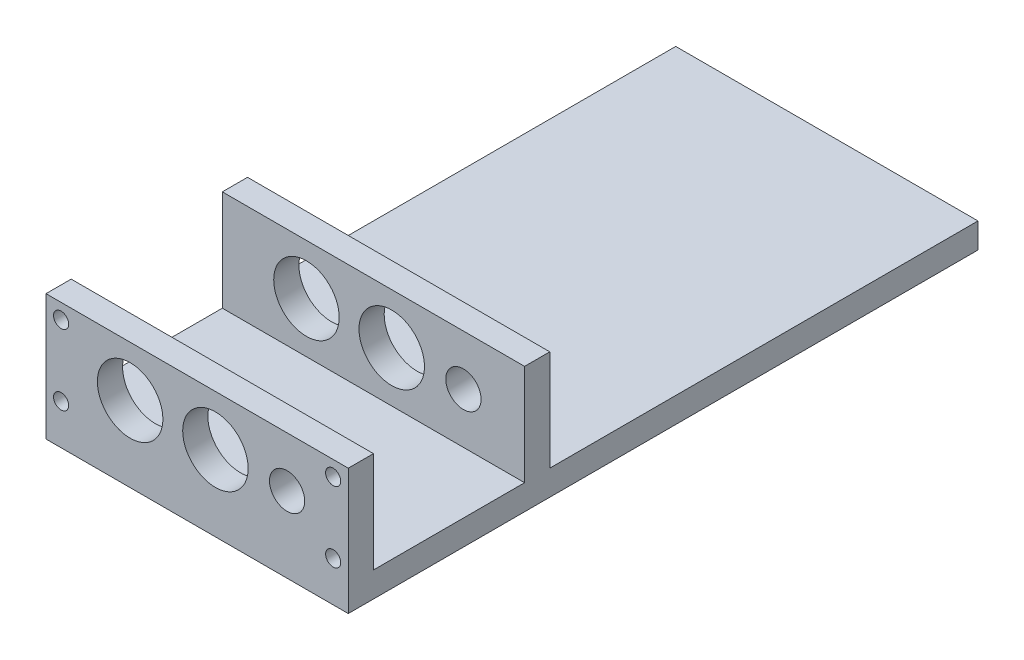
SolidWorks part; units mm, degrees
ref_plane "정면" through (0, 0, 0) normal (0, 0, 1) x (1, 0, 0)
ref_plane "윗면" through (0, 0, 0) normal (0, 1, 0) x (1, 0, 0)
ref_plane "우측면" through (0, 0, 0) normal (1, 0, 0) x (0, 0, -1)
sketch "스케치1" plane through (0, 0, 0) normal (0, 0, 1) x (1, 0, 0)
  line L0 (0, 0) -> (60, 0)
  line L3 (0, 0) -> (0, 25)
  line L4 (0, 25) -> (60, 25)
  line L5 (60, 0) -> (60, 25)
  dimension "D1" = 60
  dimension "D2" = 25
extrude "보스-돌출1" add sketch "스케치1" along normal blind 5
sketch "스케치2" plane through (0, 0, 0) normal (0, 0, -1) x (-1, 0, 0)
  line L0 (-60, 0) -> (-60, 25) construction
  line L1 (-60, 5) -> (0, 5)
  line L2 (-60, 5) -> (-60, 0)
  line L3 (-60, 0) -> (0, 0)
  line L4 (0, 5) -> (0, 0)
  dimension "D1" = 5
extrude "보스-돌출2" add sketch "스케치2" along normal blind 120
sketch "스케치3" plane through (0, 5, 0) normal (0, 1, 0) x (1, 0, 0)
  line L0 (60, 35) -> (0, 35)
  line L1 (60, 120) -> (60, 0) construction
  line L2 (0, 120) -> (0, 0) construction
  line L3 (0, 35) -> (0, 30)
  line L4 (0, 30) -> (60, 30)
  line L5 (60, 30) -> (60, 35)
  line L6 (60, -5) -> (0, -5) construction
  dimension "D1" = 40
  dimension "D2" = 5
extrude "보스-돌출3" add sketch "스케치3" along normal blind 20
sketch "스케치4" plane through (0, 0, 0) normal (0, 0, -1) x (-1, 0, 0)
  line L0 (-60, 5) -> (-60, 25) construction
  line L2 (-60, 15) -> (0, 15) construction
  line L3 (0, 25) -> (0, 5) construction
  line L4 (-30, 5) -> (-30, 25) construction
  line L5 (0, 5) -> (-60, 5) construction
  line L6 (-60, 25) -> (0, 25) construction
  circle A0 centre (-57, 22) radius 1.5
  circle A1 centre (-57, 8) radius 1.5
  circle A2 centre (-3, 22) radius 1.5
  circle A3 centre (-3, 8) radius 1.5
  dimension "D1" = 3
  dimension "D2" = 3
  dimension "D3" = 3
extrude "컷-돌출1" cut sketch "스케치4" against normal blind 20
sketch "스케치5" plane through (0, 0, 0) normal (0, 0, -1) x (-1, 0, 0)
  line L0 (-60, 15) -> (0, 15) construction
  circle A0 centre (-33.6294, 15) radius 6.5
  circle A1 centre (-16.6994, 15) radius 6.5
  point P6 (-28.3669, 15)
  point P7 (-42.738, 15)
  point P8 (-16.6994, 15)
  point P9 (-33.6294, 15)
  dimension "D1" = 13
  dimension "D2" = 13
extrude "컷-돌출2" cut sketch "스케치5" against normal through all both and the other way through all
sketch "스케치6" plane through (0, 0, 0) normal (0, 0, -1) x (-1, 0, 0)
  line L0 (-60, 15) -> (0, 15) construction
  circle A0 centre (-47.8558, 15) radius 3.5
  point P4 (-47.8558, 15)
  dimension "D1" = 7
extrude "컷-돌출3" cut sketch "스케치6" against normal through all both and the other way through all
